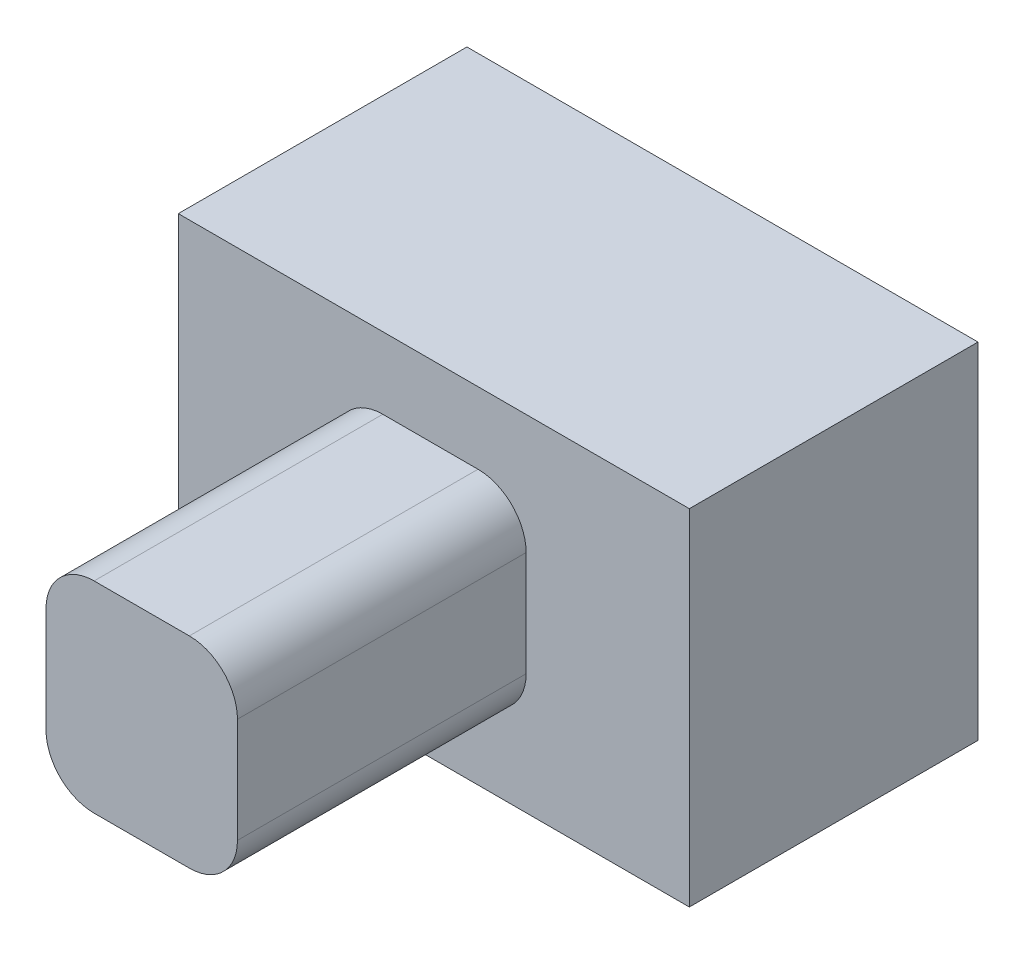
SolidWorks part; units mm, degrees
ref_plane "前视基准面" through (0, 0, 0) normal (0, 0, 1) x (1, 0, 0)
ref_plane "上视基准面" through (0, 0, 0) normal (0, 1, 0) x (1, 0, 0)
ref_plane "右视基准面" through (0, 0, 0) normal (1, 0, 0) x (0, 0, -1)
sketch "草图1" plane through (0, 0, 0) normal (0, 0, 1) x (1, 0, 0)
  line L5 (-2.4199, 4.4149) -> (8.203, 4.4149)
  line L6 (-2.4199, 4.4149) -> (-2.4199, -2.7561)
  line L7 (-2.4199, -2.7561) -> (8.203, -2.7561)
  line L8 (8.203, 4.4149) -> (8.203, -2.7561)
extrude "凸台-拉伸1" add sketch "草图1" along normal blind 6
sketch "草图2" plane through (0, 0, 6) normal (0, 0, 1) x (1, 0, 0)
  line L1 (1.8305, 2.9282) -> (3.81, 2.9282)
  line L2 (0.8305, 1.9282) -> (0.8305, -0.2528)
  line L3 (1.8305, -1.2528) -> (3.81, -1.2528)
  line L4 (4.81, 1.9282) -> (4.81, -0.2528)
  arc A0 (3.81, -1.2528) -> (4.81, -0.2528) centre (3.81, -0.2528) ccw
  arc A1 (0.8305, -0.2528) -> (1.8305, -1.2528) centre (1.8305, -0.2528) ccw
  arc A2 (1.8305, 2.9282) -> (0.8305, 1.9282) centre (1.8305, 1.9282) ccw
  arc A3 (3.81, 2.9282) -> (4.81, 1.9282) centre (3.81, 1.9282) cw
  dimension "D1" = 1
  dimension "D2" = 1
extrude "凸台-拉伸2" add sketch "草图2" along normal blind 6
sketch "草图3" plane through (0, 0, 0) normal (0, 0, -1) x (-1, 0, 0)
  line L1 (-1.8694, -0.1889) -> (-3.6194, -0.1889)
  line L2 (-1.8694, -0.1889) -> (-1.8694, 1.5611)
  line L3 (-1.8694, 1.5611) -> (-3.6194, 1.5611)
  line L4 (-3.6194, -0.1889) -> (-3.6194, 1.5611)
  dimension "D1" = 1.75
  dimension "D2" = 1.75
extrude "切除-拉伸1" cut sketch "草图3" against normal blind 4
